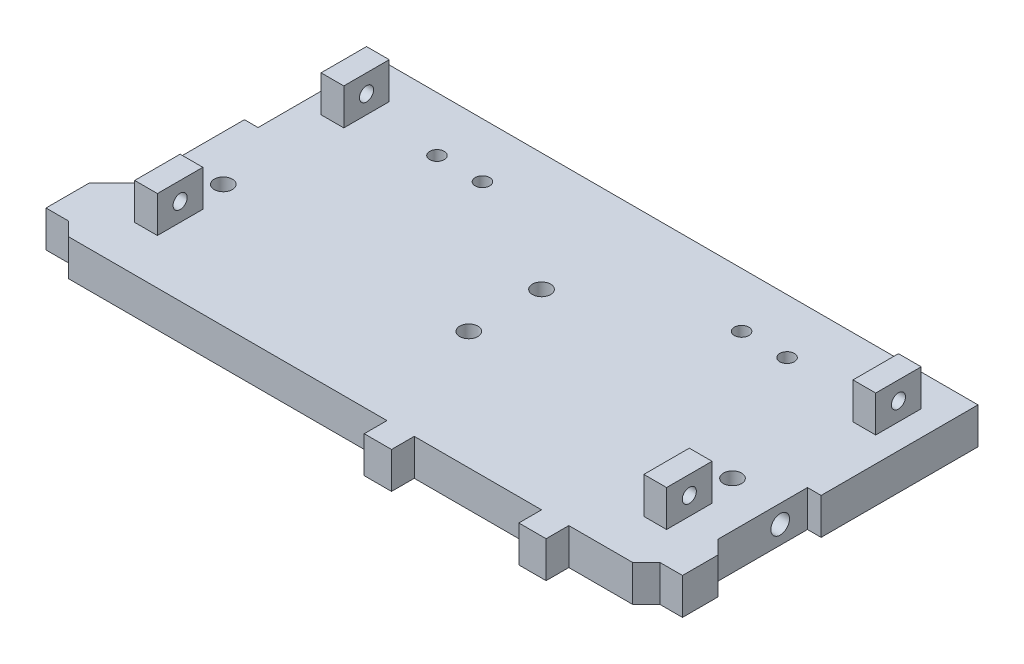
SolidWorks part; units mm, degrees
ref_plane "Front" through (0, 0, 0) normal (0, 0, 1) x (1, 0, 0)
ref_plane "Top" through (0, 0, 0) normal (0, 1, 0) x (1, 0, 0)
ref_plane "Right" through (0, 0, 0) normal (1, 0, 0) x (0, 0, -1)
sketch "Sketch1" plane through (0, 0, 0) normal (0, 1, 0) x (1, 0, 0)
  line L0 (-62, 34) -> (-62, 7.645)
  line L1 (-70, -34) -> (70, -34) construction
  line L2 (-70, -34) -> (-70, 34) construction
  line L3 (-70, 34) -> (70, 34) construction
  line L4 (70, -34) -> (70, 34) construction
  line L5 (-70, -34) -> (70, 34) construction
  line L6 (-70, 34) -> (70, -34) construction
  line L7 (-62, 7.645) -> (-65, 7.645)
  line L8 (-65, 7.645) -> (-65, -16.4271)
  line L9 (-65, -16.4271) -> (-70, -21.4271)
  line L10 (-70, -21.4271) -> (-70, -31)
  line L11 (-70, -31) -> (-65, -31)
  line L12 (-65, -31) -> (-62, -34)
  line L13 (-62, -34) -> (8, -34)
  line L14 (8, -34) -> (8, -39)
  line L15 (8, -39) -> (14, -39)
  line L16 (14, -39) -> (14, -34)
  line L17 (14, -34) -> (42, -34)
  line L18 (42, -34) -> (42, -39)
  line L19 (42, -39) -> (48, -39)
  line L20 (48, -39) -> (48, -34)
  line L21 (48, -34) -> (62, -34)
  line L22 (62, -34) -> (65, -31)
  line L23 (65, -31) -> (70, -31)
  line L24 (70, -31) -> (70, -23.1554)
  line L25 (70, -23.1554) -> (67, -20.1554)
  line L26 (67, -20.1554) -> (67, -0.5064)
  line L27 (67, -0.5064) -> (70, -0.5064)
  line L28 (70, -0.5064) -> (70, 34)
  line L29 (70, 34) -> (-70, 34)
  point P0 (0, 0)
  dimension "D1" = 68
  dimension "D2" = 140
  dimension "D3" = 45
  dimension "D4" = 135
  dimension "D5" = 3
  dimension "D6" = 6
  dimension "D7" = 6
  dimension "D8" = 28
  dimension "D9" = 45
  dimension "D10" = 135
  dimension "D11" = 5
  dimension "D12" = 5
  dimension "D13" = 3
  dimension "D14" = 5
  dimension "D15" = 19
extrude "Boss-Extrude1" add sketch "Sketch1" along normal blind 8 contours L28 L29 L0 L7 L8 L9 L10 L11 L12 L13 L14 L15 L16 L17 L18 L19 L20 L21 L22 L23 L24 L25 L26 L27
sketch "Sketch2" plane through (0, 8, 0) normal (0, 1, 0) x (1, 0, 0)
  circle A1 centre (0, 8) radius 2
  circle A2 centre (0, -8) radius 2
  dimension "D1" = 4
  dimension "D2" = 4
  dimension "D3" = 8
  dimension "D4" = 8
extrude "Cut-Extrude1" cut sketch "Sketch2" against normal through all
sketch "Sketch3" plane through (0, 8, 0) normal (0, 1, 0) x (1, 0, 0)
  line L0 (67, -20.1554) -> (67, -0.5064) construction
  line L1 (48, -34) -> (62, -34) construction
  line L2 (-62, -34) -> (8, -34) construction
  line L3 (-65, 7.645) -> (-65, -16.4271) construction
  line L4 (-62, 34) -> (-62, 7.645) construction
  line L5 (70, -0.5064) -> (70, 34) construction
  line L6 (70, 34) -> (-62, 34) construction
  circle A0 centre (57, -7) radius 2
  circle A1 centre (-55, -7) radius 2
  circle A2 centre (-37, 22) radius 1.6
  circle A3 centre (-27, 22) radius 1.6
  circle A4 centre (30, 22) radius 1.6
  circle A5 centre (40, 22) radius 1.6
  dimension "D1" = 4
  dimension "D2" = 4
  dimension "D7" = 3.2
  dimension "D8" = 3.2
  dimension "D9" = 3.2
  dimension "D10" = 3.2
  dimension "D3" = 10
  dimension "D4" = 27
  dimension "D5" = 27
  dimension "D6" = 10
  dimension "D11" = 25
  dimension "D12" = 10
  dimension "D13" = 10
  dimension "D14" = 30
  dimension "D15" = 12
extrude "Cut-Extrude2" cut sketch "Sketch3" against normal through all contours A0 | A2 | A3 | A4 | A5 | A1
sketch "Sketch4" plane through (67, 0, 0) normal (1, 0, 0) x (0, 0, -1)
  line L0 (-0.5064, 8) -> (-0.5064, 0) construction
  line L1 (-0.5064, 4) -> (-6.5064, 4) construction
  circle A0 centre (-6.5064, 4) radius 2.05
  dimension "D1" = 4.1
  dimension "D2" = 6
extrude "Cut-Extrude3" cut sketch "Sketch4" against normal blind 6
sketch "Sketch5" plane through (0, 8, 0) normal (0, 1, 0) x (1, 0, 0)
  line L0 (-62, 34) -> (-62, 7.645) construction
  line L1 (-57.5, -24) -> (-52.5, -24)
  line L2 (-57.5, -24) -> (-57.5, -14)
  line L3 (-57.5, -14) -> (-52.5, -14)
  line L4 (-52.5, -24) -> (-52.5, -14)
  line L5 (-57.5, -24) -> (-52.5, -14) construction
  line L6 (-57.5, -14) -> (-52.5, -24) construction
  line L7 (-62, -34) -> (8, -34) construction
  line L8 (70, 34) -> (-62, 34) construction
  line L9 (-57.5, 27) -> (-52.5, 27)
  line L10 (-57.5, 27) -> (-57.5, 17)
  line L11 (-57.5, 17) -> (-52.5, 17)
  line L12 (-52.5, 27) -> (-52.5, 17)
  line L13 (-57.5, 27) -> (-52.5, 17) construction
  line L14 (-57.5, 17) -> (-52.5, 27) construction
  line L15 (67, -20.1554) -> (67, -0.5064) construction
  line L16 (54.5, -24) -> (59.5, -24)
  line L17 (54.5, -24) -> (54.5, -14)
  line L18 (54.5, -14) -> (59.5, -14)
  line L19 (59.5, -24) -> (59.5, -14)
  line L20 (54.5, -24) -> (59.5, -14) construction
  line L21 (54.5, -14) -> (59.5, -24) construction
  line L22 (59.5, 27) -> (64.5, 27)
  line L23 (59.5, 27) -> (59.5, 17)
  line L24 (59.5, 17) -> (64.5, 17)
  line L25 (64.5, 27) -> (64.5, 17)
  line L26 (59.5, 27) -> (64.5, 17) construction
  line L27 (59.5, 17) -> (64.5, 27) construction
  line L28 (48, -34) -> (62, -34) construction
  line L30 (70, -0.5064) -> (70, 34) construction
  point P0 (-55, -19)
  point P9 (-55, 22)
  point P16 (57, -19)
  point P21 (62, 22)
  dimension "D1" = 10
  dimension "D2" = 5
  dimension "D3" = 4.5
  dimension "D4" = 10
  dimension "D5" = 10
  dimension "D6" = 5
  dimension "D7" = 7
  dimension "D8" = 4.5
  dimension "D9" = 10
  dimension "D10" = 5
  dimension "D11" = 10
  dimension "D12" = 5
  dimension "D13" = 7.5
  dimension "D14" = 10
  dimension "D15" = 5.5
  dimension "D16" = 7
extrude "Boss-Extrude2" add sketch "Sketch5" along normal blind 8
sketch "Sketch6" plane through (-57.5, 0, 0) normal (-1, 0, 0) x (0, 0, 1)
  line L0 (14, 8) -> (24, 16) construction
  line L1 (-27, 8) -> (-17, 16) construction
  circle A0 centre (-22, 12) radius 1.55
  circle A1 centre (19, 12) radius 1.55
  dimension "D1" = 3.1
  dimension "D2" = 3.1
extrude "Cut-Extrude4" cut sketch "Sketch6" against normal through all
